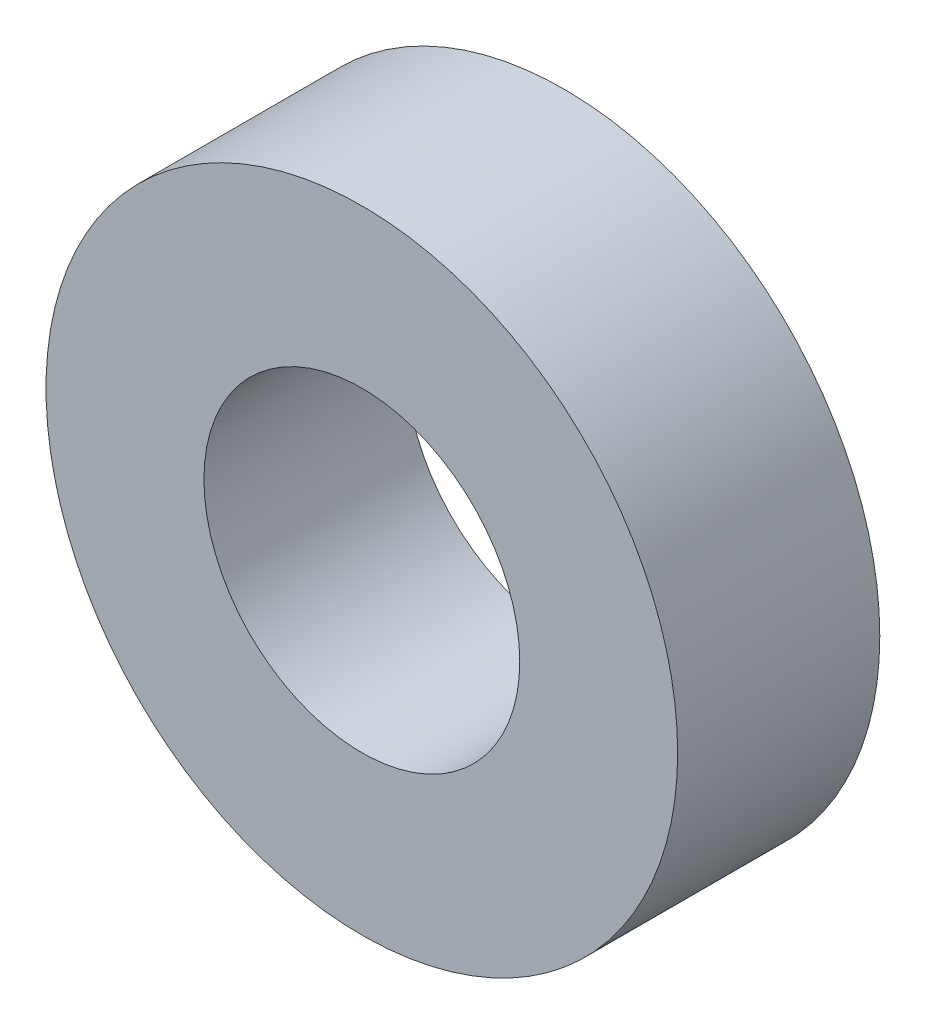
SolidWorks part; units mm, degrees
ref_plane "Plan de face" through (0, 0, 0) normal (0, 0, 1) x (1, 0, 0)
ref_plane "Plan de dessus" through (0, 0, 0) normal (0, 1, 0) x (1, 0, 0)
ref_plane "Plan de droite" through (0, 0, 0) normal (1, 0, 0) x (0, 0, -1)
sketch "Esquisse1" plane through (0, 0, 0) normal (0, 0, 1) x (1, 0, 0)
  circle A0 centre (0, 0) radius 12.5
  circle A1 centre (0, 0) radius 6.25
  dimension "D1" = 12.5
  dimension "D2" = 25
extrude "Boss.-Extru.1" add sketch "Esquisse1" along normal blind 8
